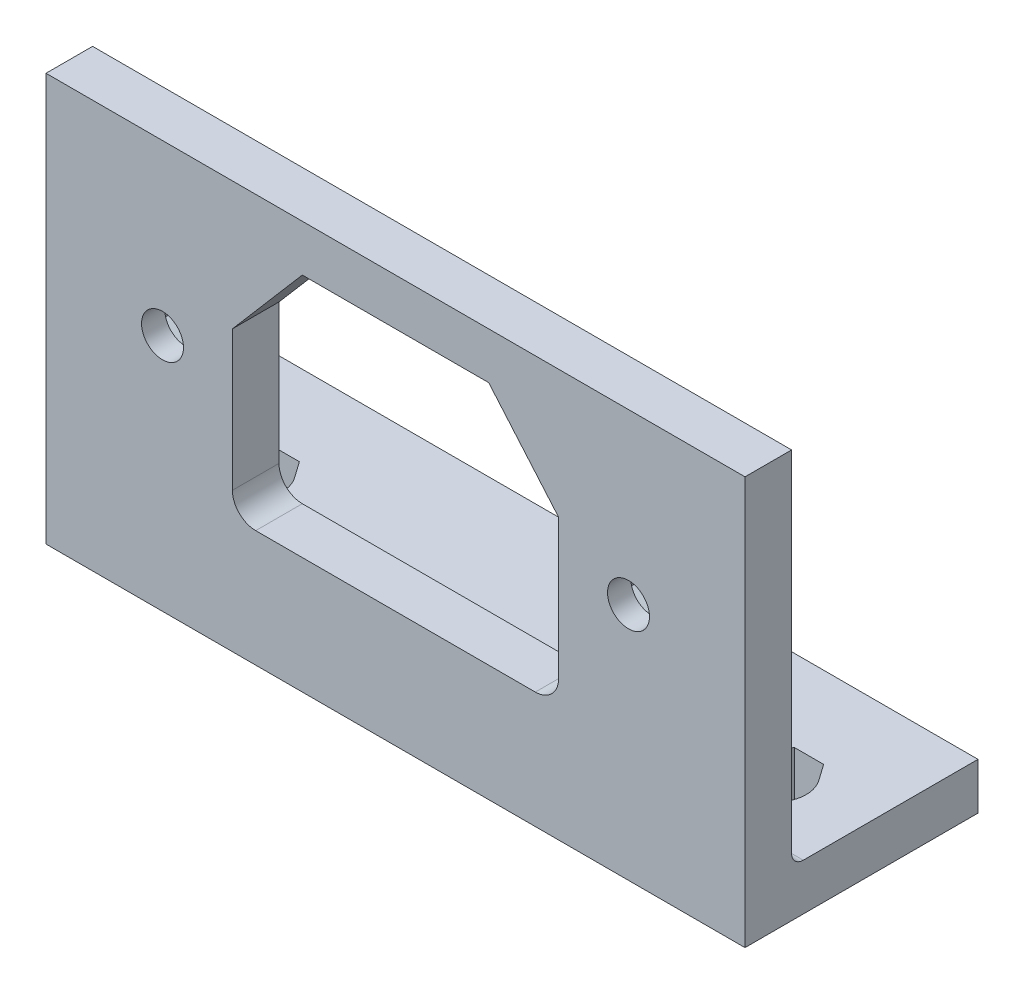
SolidWorks part; units mm, degrees
ref_plane "Alzado" through (0, 0, 0) normal (0, 0, 1) x (1, 0, 0)
ref_plane "Planta" through (0, 0, 0) normal (0, 1, 0) x (1, 0, 0)
ref_plane "Vista lateral" through (0, 0, 0) normal (1, 0, 0) x (0, 0, -1)
sketch "Croquis1" plane through (0, 0, 0) normal (1, 0, 0) x (0, 0, -1)
  line L0 (0, 0) -> (0, 35)
  line L1 (0, 35) -> (4, 35)
  line L2 (4, 35) -> (4, 4)
  line L3 (4, 4) -> (20, 4)
  line L4 (20, 4) -> (20, 0)
  line L5 (20, 0) -> (0, 0)
  dimension "D1" = 35
  dimension "D2" = 16
  dimension "D3" = 4
  dimension "D4" = 4
extrude "Saliente-Extruir1" add sketch "Croquis1" along normal mid plane 60
sketch "Croquis2" plane through (0, 0, 0) normal (0, 0, 1) x (1, 0, 0)
  line L0 (-12, 10) -> (12, 10)
  line L1 (14, 12) -> (14, 24)
  line L2 (14, 24) -> (8, 31)
  line L3 (8, 31) -> (-8, 31)
  line L4 (-8, 31) -> (-14, 24)
  line L5 (-14, 24) -> (-14, 12)
  line L6 (0, 39.8326) -> (0, -5.3106) construction
  line L7 (30, 35) -> (-30, 35) construction
  line L8 (-30.0293, 20.5) -> (34.0741, 20.5) construction
  arc A0 (14, 12) -> (12, 10) centre (12, 12) cw
  arc A1 (-12, 10) -> (-14, 12) centre (-12, 12) cw
  circle A2 centre (-20, 20.5) radius 1.8
  circle A3 centre (20, 20.5) radius 1.8
  point P13 (14, 10)
  point P16 (-14, 10)
  dimension "D6" = 2
  dimension "D7" = 3.6
  dimension "D1" = 28
  dimension "D2" = 21
  dimension "D3" = 16
  dimension "D4" = 14
  dimension "D5" = 4
  dimension "D8" = 40
  dimension "D9" = 10.5
extrude "Cortar-Extruir1" cut sketch "Croquis2" against normal through all
sketch "Croquis3" plane through (0, 0, 0) normal (0, -1, 0) x (1, 0, 0)
  line L0 (0, 9.2522) -> (0, -25.747) construction
  line L1 (30, 0) -> (-30, 0) construction
  line L2 (-22.5, -5.2262) -> (-22.5, -14.7736) construction
  line L3 (-24.7478, -11.5842) -> (-23.75, -13)
  line L4 (-23.75, -13) -> (-21.25, -13)
  line L5 (-21.25, -13) -> (-20.2522, -11.5842)
  line L6 (22.5, -4.2455) -> (22.5, -16.8816) construction
  line L7 (20.2522, -11.5842) -> (21.25, -13)
  line L8 (21.25, -13) -> (23.75, -13)
  line L9 (23.75, -13) -> (24.7478, -11.5842)
  arc A0 (-20.2522, -11.5842) -> (-24.7478, -11.5842) centre (-22.5, -10) ccw
  arc A1 (24.7478, -11.5842) -> (20.2522, -11.5842) centre (22.5, -10) ccw
  dimension "D3" = 5.5
  dimension "D1" = 45
  dimension "D2" = 10
  dimension "D4" = 2.5
  dimension "D5" = 3
  dimension "D6" = 2.5
  dimension "D7" = 3
extrude "Cortar-Extruir2" cut sketch "Croquis3" against normal through all
fillet "Redondeo1" radius 1 1 edges at (0, 4, -4)
sketch "Croquis4" plane through (0, 0, -4) normal (0, 0, -1) x (-1, 0, 0)
  line L1 (-17, 18.7679) -> (-17, 22.2321)
  line L2 (-17, 22.2321) -> (-20, 23.9641)
  line L3 (-20, 23.9641) -> (-23, 22.2321)
  line L4 (-23, 22.2321) -> (-23, 18.7679)
  line L5 (-23, 18.7679) -> (-20, 17.0359)
  line L6 (-20, 17.0359) -> (-17, 18.7679)
  line L7 (17, 18.7679) -> (20, 17.0359)
  line L8 (20, 17.0359) -> (23, 18.7679)
  line L9 (23, 18.7679) -> (23, 22.2321)
  line L10 (23, 22.2321) -> (20, 23.9641)
  line L11 (20, 23.9641) -> (17, 22.2321)
  line L12 (17, 22.2321) -> (17, 18.7679)
  circle A0 centre (-20, 20.5) radius 3 construction
  circle A1 centre (20, 20.5) radius 3 construction
  dimension "D1" = 6
extrude "Cortar-Extruir3" cut sketch "Croquis4" against normal blind 2
